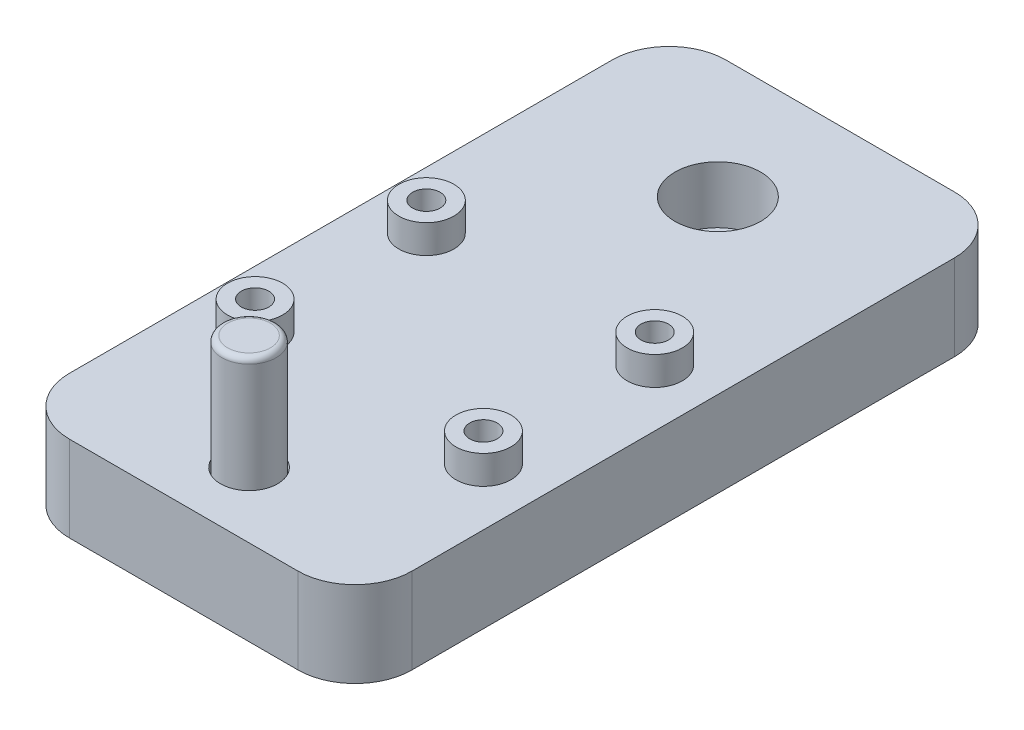
SolidWorks part; units mm, degrees
ref_plane "Front Plane" through (0, 0, 0) normal (0, 0, 1) x (1, 0, 0)
ref_plane "Top Plane" through (0, 0, 0) normal (0, 1, 0) x (1, 0, 0)
ref_plane "Right Plane" through (0, 0, 0) normal (1, 0, 0) x (0, 0, -1)
sketch "Sketch1" plane through (0, 0, 0) normal (0, 1, 0) x (1, 0, 0)
  line L1 (0, 0) -> (60, 0)
  line L2 (0, 0) -> (0, 115)
  line L3 (0, 115) -> (60, 115)
  line L4 (60, 0) -> (60, 115)
  dimension "D1" = 60
  dimension "D2" = 115
extrude "Boss-Extrude1" add sketch "Sketch1" along normal blind 15
sketch "Sketch2" plane through (0, 15, 0) normal (0, 1, 0) x (1, 0, 0)
  line L0 (0, 57.5) -> (60, 57.5) construction
  line L3 (0, 115) -> (0, 0) construction
  line L4 (60, 0) -> (60, 115) construction
  line L5 (30, 57.5) -> (30, 74.6395) construction
  circle A0 centre (30, 93.55) radius 7.5
  circle A1 centre (30, 11.45) radius 5
  dimension "D3" = 10
  dimension "D4" = 15
  dimension "D1" = 36.05
  dimension "D2" = 46.05
  dimension "D5" = 57.5
extrude "Cut-Extrude1" cut sketch "Sketch2" against normal blind 10
sketch "Sketch3" plane through (0, 0, 0) normal (0, -1, 0) x (-1, 0, 0)
  line L0 (0, 115) -> (0, 0) construction
  line L1 (-60, 115) -> (0, 115) construction
  circle A0 centre (-30, 57.5) radius 5
  dimension "D1" = 10
  dimension "D2" = 30
  dimension "D3" = 57.5
extrude "Cut-Extrude2" cut sketch "Sketch3" against normal blind 14.5
sketch "Sketch4" plane through (0, 5, 0) normal (0, 1, 0) x (1, 0, 0)
  circle A0 centre (30, 11.45) radius 4.75
  dimension "D1" = 9.5
extrude "Boss-Extrude2" add sketch "Sketch4" along normal blind 30
fillet "Fillet1" radius 1 1 edges at (30, 35, -6.7)
fillet "Fillet2" radius 10 4 edges at (0, 7.5, -115) (60, 7.5, -115) (60, 7.5, 0) (0, 7.5, 0)
sketch "Sketch5" plane through (0, 15, 0) normal (0, 1, 0) x (1, 0, 0)
  line L0 (0, 57.5) -> (60, 57.5) construction
  line L1 (0, 105) -> (0, 10) construction
  line L2 (60, 10) -> (60, 105) construction
  line L3 (60, 57.5) -> (30, 57.5) construction
  line L4 (30, 57.5) -> (30, 93.55) construction
  circle A0 centre (50, 62.5) radius 2.413
  circle A1 centre (50, 32.5) radius 2.413
  circle A2 centre (10, 32.5) radius 2.413
  circle A3 centre (10, 62.5) radius 2.413
  circle A4 centre (50, 62.5) radius 4.826
  circle A5 centre (50, 32.5) radius 4.826
  circle A6 centre (10, 32.5) radius 4.826
  circle A7 centre (10, 62.5) radius 4.826
  dimension "D1" = 4.826
  dimension "D2" = 4.826
  dimension "D3" = 4.826
  dimension "D4" = 4.826
  dimension "D10" = 9.652
  dimension "D11" = 9.652
  dimension "D12" = 9.652
  dimension "D13" = 9.652
  dimension "D5" = 20
  dimension "D6" = 20
  dimension "D7" = 5
  dimension "D8" = 25
  dimension "D9" = 57.5
extrude "Boss-Extrude3" add sketch "Sketch5" along normal blind 5
